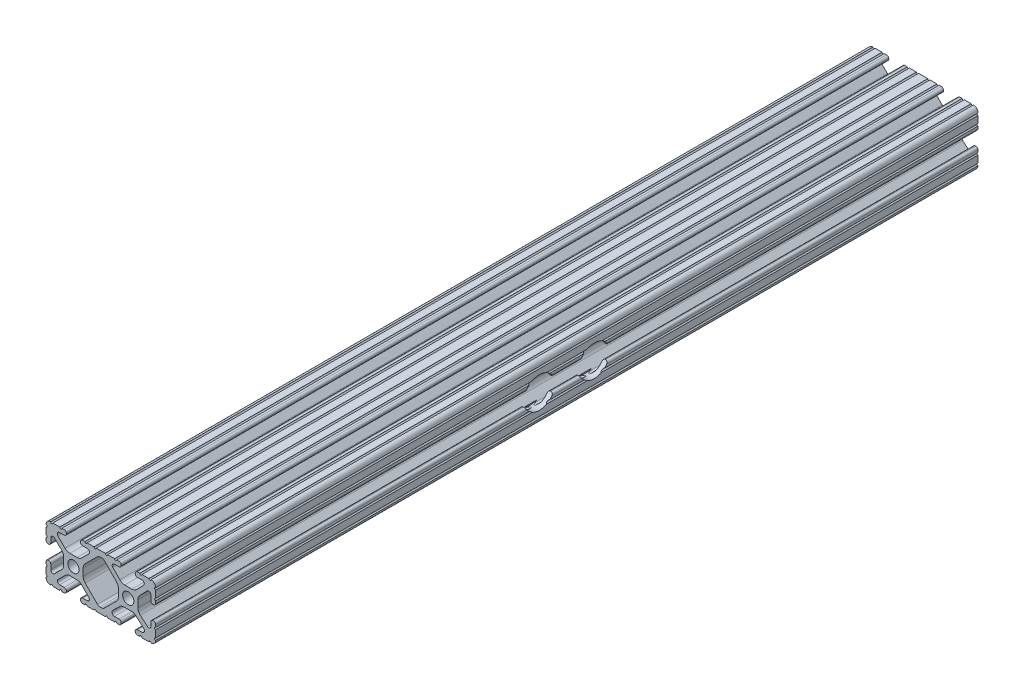
SolidWorks part; units mm, degrees
ref_plane "Front Plane" through (0, 0, 0) normal (0, 0, 1) x (1, 0, 0)
ref_plane "Top Plane" through (0, 0, 0) normal (0, 1, 0) x (1, 0, 0)
ref_plane "Right Plane" through (0, 0, 0) normal (1, 0, 0) x (0, 0, -1)
sketch "Sketch1" plane through (0, 0, 0) normal (0, 0, 1) x (1, 0, 0)
  line L0 (-7.2595, -3.8694) -> (-1.5457, -9.5728)
  line L1 (-8.1915, 1.6223) -> (-8.1915, -1.6223)
  line L2 (-1.504, 9.5765) -> (-7.252, 3.8768)
  line L3 (0.5515, 10.033) -> (-0.3952, 10.033)
  line L4 (7.2829, 3.8459) -> (1.6756, 9.5611)
  line L5 (8.1915, -1.6223) -> (8.1915, 1.6223)
  line L6 (1.5457, -9.5728) -> (7.2595, -3.8694)
  line L7 (-0.4332, -10.033) -> (0.4332, -10.033)
  line L8 (18.0171, 12.7) -> (16.9875, 12.7)
  line L9 (15.9385, 11.651) -> (15.9385, 11.5392)
  line L10 (16.9875, 10.4902) -> (19.1164, 10.4902)
  line L11 (19.8441, 8.7652) -> (16.619, 5.4551)
  line L12 (14.3449, 4.4958) -> (11.0833, 4.4958)
  line L13 (8.817, 5.4472) -> (5.5642, 8.7627)
  line L14 (6.2894, 10.4902) -> (8.4125, 10.4902)
  line L15 (9.4615, 11.5392) -> (9.4615, 11.651)
  line L16 (8.4125, 12.7) -> (7.3829, 12.7)
  line L17 (6.3669, 12.7) -> (3.1496, 12.7)
  line L18 (2.1336, 12.7) -> (-2.1336, 12.7)
  line L19 (-3.1496, 12.7) -> (-6.3669, 12.7)
  line L20 (-7.3829, 12.7) -> (-8.4125, 12.7)
  line L21 (-9.4615, 11.651) -> (-9.4615, 11.5392)
  line L22 (-8.4125, 10.4902) -> (-6.2836, 10.4902)
  line L23 (-5.5326, 8.6661) -> (-8.81, 5.4163)
  line L24 (-11.0455, 4.4958) -> (-14.3545, 4.4958)
  line L25 (-16.59, 5.4163) -> (-19.8674, 8.6661)
  line L26 (-19.1164, 10.4902) -> (-16.9875, 10.4902)
  line L27 (-15.9385, 11.5392) -> (-15.9385, 11.651)
  line L28 (-16.9875, 12.7) -> (-18.0171, 12.7)
  line L29 (-19.0331, 12.7) -> (-22.2504, 12.7)
  line L30 (-25.4, 9.5504) -> (-25.4, 6.3331)
  line L31 (-25.4, 5.3171) -> (-25.4, 4.2375)
  line L32 (-24.401, 3.2385) -> (-24.2392, 3.2385)
  line L33 (-23.1902, 4.2875) -> (-23.1902, 6.3347)
  line L34 (-21.434, 7.0665) -> (-18.148, 3.8082)
  line L35 (-17.2085, 1.5536) -> (-17.2085, -1.6952)
  line L36 (-18.1405, -3.9423) -> (-21.4316, -7.2274)
  line L37 (-23.1902, -6.498) -> (-23.1902, -4.2875)
  line L38 (-24.2392, -3.2385) -> (-24.351, -3.2385)
  line L39 (-25.4, -4.2875) -> (-25.4, -5.3171)
  line L40 (-25.4, -6.3331) -> (-25.4, -9.5504)
  line L41 (-22.2504, -12.7) -> (-19.0331, -12.7)
  line L42 (-18.0171, -12.7) -> (-16.9875, -12.7)
  line L43 (-15.9384, -11.651) -> (-15.9384, -11.5392)
  line L44 (-16.9875, -10.4902) -> (-19.1164, -10.4902)
  line L45 (-19.8341, -8.7551) -> (-16.4966, -5.4237)
  line L46 (-14.2536, -4.4958) -> (-11.1464, -4.4958)
  line L47 (-8.9034, -5.4237) -> (-5.5659, -8.7551)
  line L48 (-6.2836, -10.4902) -> (-8.4125, -10.4902)
  line L49 (-9.4616, -11.5392) -> (-9.4616, -11.651)
  line L50 (-8.4125, -12.7) -> (-7.3829, -12.7)
  line L51 (-6.3669, -12.7) -> (-3.1496, -12.7)
  line L52 (-2.1336, -12.7) -> (2.1336, -12.7)
  line L53 (3.1496, -12.7) -> (6.3669, -12.7)
  line L54 (7.3829, -12.7) -> (8.4125, -12.7)
  line L55 (9.4616, -11.651) -> (9.4616, -11.5392)
  line L56 (8.4125, -10.4902) -> (6.2894, -10.4902)
  line L57 (5.4807, -8.5353) -> (8.5979, -5.4237)
  line L58 (10.8409, -4.4958) -> (14.1026, -4.4958)
  line L59 (16.1879, -5.2766) -> (19.8682, -8.4822)
  line L60 (19.1164, -10.4902) -> (16.9875, -10.4902)
  line L61 (15.9384, -11.5392) -> (15.9384, -11.651)
  line L62 (16.9875, -12.7) -> (18.0171, -12.7)
  line L63 (19.0331, -12.7) -> (22.2504, -12.7)
  line L64 (25.4, -9.5504) -> (25.4, -6.3331)
  line L65 (25.4, -5.3171) -> (25.4, -4.2375)
  line L66 (24.401, -3.2385) -> (24.1892, -3.2385)
  line L67 (23.1902, -4.2375) -> (23.1902, -6.1559)
  line L68 (21.584, -6.8869) -> (18.2982, -4.025)
  line L69 (17.2085, -1.6308) -> (17.2085, 1.6308)
  line L70 (18.1094, 3.8465) -> (21.5263, 7.3534)
  line L71 (23.1902, 6.6769) -> (23.1902, 4.2375)
  line L72 (24.1892, 3.2385) -> (24.401, 3.2385)
  line L73 (25.4, 4.2375) -> (25.4, 5.3171)
  line L74 (25.4, 6.3332) -> (25.4, 9.5504)
  line L75 (22.2504, 12.7) -> (19.0331, 12.7)
  circle A0 centre (-12.7, 0) radius 2.6035
  circle A1 centre (12.7, 0) radius 2.6035
  arc A2 (-1.5457, -9.5728) -> (-0.4332, -10.033) centre (-0.4332, -8.4582) ccw
  arc A3 (-8.1915, -1.6223) -> (-7.2595, -3.8694) centre (-5.0165, -1.6223) ccw
  arc A4 (-7.252, 3.8768) -> (-8.1915, 1.6223) centre (-5.0165, 1.6223) ccw
  arc A5 (-0.3952, 10.033) -> (-1.504, 9.5765) centre (-0.3952, 8.4582) ccw
  arc A6 (1.6756, 9.5611) -> (0.5515, 10.033) centre (0.5515, 8.4582) ccw
  arc A7 (8.1915, 1.6223) -> (7.2829, 3.8459) centre (5.0165, 1.6223) ccw
  arc A8 (7.2595, -3.8694) -> (8.1915, -1.6223) centre (5.0165, -1.6223) ccw
  arc A9 (0.4332, -10.033) -> (1.5457, -9.5728) centre (0.4332, -8.4582) ccw
  arc A10 (18.0171, 12.7) -> (19.0331, 12.7) centre (18.5251, 12.7) ccw
  arc A11 (16.9875, 12.7) -> (15.9385, 11.651) centre (16.9875, 11.651) ccw
  arc A12 (15.9385, 11.5392) -> (16.9875, 10.4902) centre (16.9875, 11.5392) ccw
  arc A13 (19.8441, 8.7652) -> (19.1164, 10.4902) centre (19.1164, 9.4742) ccw
  arc A14 (14.3449, 4.4958) -> (16.619, 5.4551) centre (14.3449, 7.6708) ccw
  arc A15 (8.817, 5.4472) -> (11.0833, 4.4958) centre (11.0833, 7.6708) ccw
  arc A16 (6.2894, 10.4902) -> (5.5642, 8.7627) centre (6.2894, 9.4742) ccw
  arc A17 (8.4125, 10.4902) -> (9.4615, 11.5392) centre (8.4125, 11.5392) ccw
  arc A18 (9.4615, 11.651) -> (8.4125, 12.7) centre (8.4125, 11.651) ccw
  arc A19 (6.3669, 12.7) -> (7.3829, 12.7) centre (6.8749, 12.7) ccw
  arc A20 (2.1336, 12.7) -> (3.1496, 12.7) centre (2.6416, 12.7) ccw
  arc A21 (-3.1496, 12.7) -> (-2.1336, 12.7) centre (-2.6416, 12.7) ccw
  arc A22 (-7.3829, 12.7) -> (-6.3669, 12.7) centre (-6.8749, 12.7) ccw
  arc A23 (-8.4125, 12.7) -> (-9.4615, 11.651) centre (-8.4125, 11.651) ccw
  arc A24 (-9.4615, 11.5392) -> (-8.4125, 10.4902) centre (-8.4125, 11.5392) ccw
  arc A25 (-5.5326, 8.6661) -> (-6.2836, 10.4902) centre (-6.2836, 9.4235) ccw
  arc A26 (-11.0455, 4.4958) -> (-8.81, 5.4163) centre (-11.0455, 7.6708) ccw
  arc A27 (-16.59, 5.4163) -> (-14.3545, 4.4958) centre (-14.3545, 7.6708) ccw
  arc A28 (-19.1164, 10.4902) -> (-19.8674, 8.6661) centre (-19.1164, 9.4235) ccw
  arc A29 (-16.9875, 10.4902) -> (-15.9385, 11.5392) centre (-16.9875, 11.5392) ccw
  arc A30 (-15.9385, 11.651) -> (-16.9875, 12.7) centre (-16.9875, 11.651) ccw
  arc A31 (-19.0331, 12.7) -> (-18.0171, 12.7) centre (-18.5251, 12.7) ccw
  arc A32 (-23.2664, 12.6998) -> (-22.2504, 12.7) centre (-22.7584, 12.7) ccw
  arc A33 (-23.2664, 12.6998) -> (-25.3998, 10.5664) centre (-23.2918, 10.5918) ccw
  arc A34 (-25.4, 9.5504) -> (-25.3998, 10.5664) centre (-25.4, 10.0584) ccw
  arc A35 (-25.4, 5.3171) -> (-25.4, 6.3331) centre (-25.4, 5.8251) ccw
  arc A36 (-25.4, 4.2375) -> (-24.401, 3.2385) centre (-24.401, 4.2375) ccw
  arc A37 (-24.2392, 3.2385) -> (-23.1902, 4.2875) centre (-24.2392, 4.2875) ccw
  arc A38 (-21.434, 7.0665) -> (-23.1902, 6.3347) centre (-22.1596, 6.3347) ccw
  arc A39 (-17.2085, 1.5536) -> (-18.148, 3.8082) centre (-20.3835, 1.5536) ccw
  arc A40 (-18.1405, -3.9423) -> (-17.2085, -1.6952) centre (-20.3835, -1.6952) ccw
  arc A41 (-23.1902, -6.498) -> (-21.4316, -7.2274) centre (-22.1596, -6.498) ccw
  arc A42 (-23.1902, -4.2875) -> (-24.2392, -3.2385) centre (-24.2392, -4.2875) ccw
  arc A43 (-24.351, -3.2385) -> (-25.4, -4.2875) centre (-24.351, -4.2875) ccw
  arc A44 (-25.4, -6.3331) -> (-25.4, -5.3171) centre (-25.4, -5.8251) ccw
  arc A45 (-25.3998, -10.5664) -> (-25.4, -9.5504) centre (-25.4, -10.0584) ccw
  arc A46 (-25.3998, -10.5664) -> (-23.2664, -12.6998) centre (-23.2918, -10.5918) ccw
  arc A47 (-22.2504, -12.7) -> (-23.2664, -12.6998) centre (-22.7584, -12.7) ccw
  arc A48 (-18.0171, -12.7) -> (-19.0331, -12.7) centre (-18.5251, -12.7) ccw
  arc A49 (-16.9875, -12.7) -> (-15.9384, -11.651) centre (-16.9875, -11.651) ccw
  arc A50 (-15.9384, -11.5392) -> (-16.9875, -10.4902) centre (-16.9875, -11.5392) ccw
  arc A51 (-19.8341, -8.7551) -> (-19.1164, -10.4902) centre (-19.1164, -9.4742) ccw
  arc A52 (-14.2536, -4.4958) -> (-16.4966, -5.4237) centre (-14.2536, -7.6708) ccw
  arc A53 (-8.9034, -5.4237) -> (-11.1464, -4.4958) centre (-11.1464, -7.6708) ccw
  arc A54 (-6.2836, -10.4902) -> (-5.5659, -8.7551) centre (-6.2836, -9.4742) ccw
  arc A55 (-8.4125, -10.4902) -> (-9.4616, -11.5392) centre (-8.4125, -11.5392) ccw
  arc A56 (-9.4616, -11.651) -> (-8.4125, -12.7) centre (-8.4125, -11.651) ccw
  arc A57 (-6.3669, -12.7) -> (-7.3829, -12.7) centre (-6.8749, -12.7) ccw
  arc A58 (-2.1336, -12.7) -> (-3.1496, -12.7) centre (-2.6416, -12.7) ccw
  arc A59 (3.1496, -12.7) -> (2.1336, -12.7) centre (2.6416, -12.7) ccw
  arc A60 (7.3829, -12.7) -> (6.3669, -12.7) centre (6.8749, -12.7) ccw
  arc A61 (8.4125, -12.7) -> (9.4616, -11.651) centre (8.4125, -11.651) ccw
  arc A62 (9.4616, -11.5392) -> (8.4125, -10.4902) centre (8.4125, -11.5392) ccw
  arc A63 (5.4807, -8.5353) -> (6.2894, -10.4902) centre (6.2894, -9.3455) ccw
  arc A64 (10.8409, -4.4958) -> (8.5979, -5.4237) centre (10.8409, -7.6708) ccw
  arc A65 (16.1879, -5.2766) -> (14.1026, -4.4958) centre (14.1026, -7.6708) ccw
  arc A66 (19.1164, -10.4902) -> (19.8682, -8.4822) centre (19.1164, -9.3455) ccw
  arc A67 (16.9875, -10.4902) -> (15.9384, -11.5392) centre (16.9875, -11.5392) ccw
  arc A68 (15.9384, -11.651) -> (16.9875, -12.7) centre (16.9875, -11.651) ccw
  arc A69 (19.0331, -12.7) -> (18.0171, -12.7) centre (18.5251, -12.7) ccw
  arc A70 (23.2664, -12.6998) -> (22.2504, -12.7) centre (22.7584, -12.7) ccw
  arc A71 (23.2664, -12.6998) -> (25.3998, -10.5664) centre (23.2918, -10.5918) ccw
  arc A72 (25.4, -9.5504) -> (25.3998, -10.5664) centre (25.4, -10.0584) ccw
  arc A73 (25.4, -5.3171) -> (25.4, -6.3331) centre (25.4, -5.8251) ccw
  arc A74 (25.4, -4.2375) -> (24.401, -3.2385) centre (24.401, -4.2375) ccw
  arc A75 (24.1892, -3.2385) -> (23.1902, -4.2375) centre (24.1892, -4.2375) ccw
  arc A76 (21.584, -6.8869) -> (23.1902, -6.1559) centre (22.2207, -6.1559) ccw
  arc A77 (17.2085, -1.6308) -> (18.2982, -4.025) centre (20.3835, -1.6308) ccw
  arc A78 (18.1094, 3.8465) -> (17.2085, 1.6308) centre (20.3835, 1.6308) ccw
  arc A79 (23.1902, 6.6769) -> (21.5263, 7.3534) centre (22.2207, 6.6769) ccw
  arc A80 (23.1902, 4.2375) -> (24.1892, 3.2385) centre (24.1892, 4.2375) ccw
  arc A81 (24.401, 3.2385) -> (25.4, 4.2375) centre (24.401, 4.2375) ccw
  arc A82 (25.4, 6.3332) -> (25.4, 5.3171) centre (25.4, 5.8251) ccw
  arc A83 (25.3998, 10.5664) -> (25.4, 9.5504) centre (25.4, 10.0584) ccw
  arc A84 (25.3998, 10.5664) -> (23.2664, 12.6998) centre (23.2918, 10.5918) ccw
  arc A85 (22.2504, 12.7) -> (23.2664, 12.6998) centre (22.7584, 12.7) ccw
  point P248 (0, 10.033)
extrude "Boss-Extrude1" add sketch "Sketch1" along normal mid plane 381
hole_wizard "CBORE for 1/4 Binding Head Machine Screw1" positions "Sketch2" profile "Sketch4" counterbore size "1/4" standard "ANSI Inch" end condition through all
sketch "Sketch2" plane through (25.4, 0, 0) normal (1, 0, 0) x (0, 0, -1)
  line L0 (-12.7, 0) -> (12.7, 0) construction
  line L2 (-190.5, 12.6998) -> (190.5, 12.6998) construction
  line L4 (0, 12.6998) -> (0, 0) construction
  point P0 (-12.7, 0)
  point P2 (12.7, 0)
  point P19 (0, 0)
  dimension "D1" = 25.4
sketch "Sketch4" plane through (25.4, 0, 12.7) normal (0, 1, 0) x (0, 0, -1)
  line L0 (0, 0) -> (0, 50.8)
  line L1 (0, 50.8) -> (3.3782, 50.8)
  line L3 (3.3782, 50.8) -> (3.3782, 4.191)
  line L4 (3.3782, 4.191) -> (7.1437, 4.191)
  line L5 (7.1437, 4.191) -> (7.1437, 0)
  line L7 (7.1437, 0) -> (0, 0)
  line L11 (0, -6.35) -> (0, 107.95) construction
  dimension "Thru Hole Dia." = 6.7564
  dimension "Thru Hole Depth" = 50.8
  dimension "C'Bore Dia." = 14.2875
  dimension "C'Bore Depth" = 4.191
